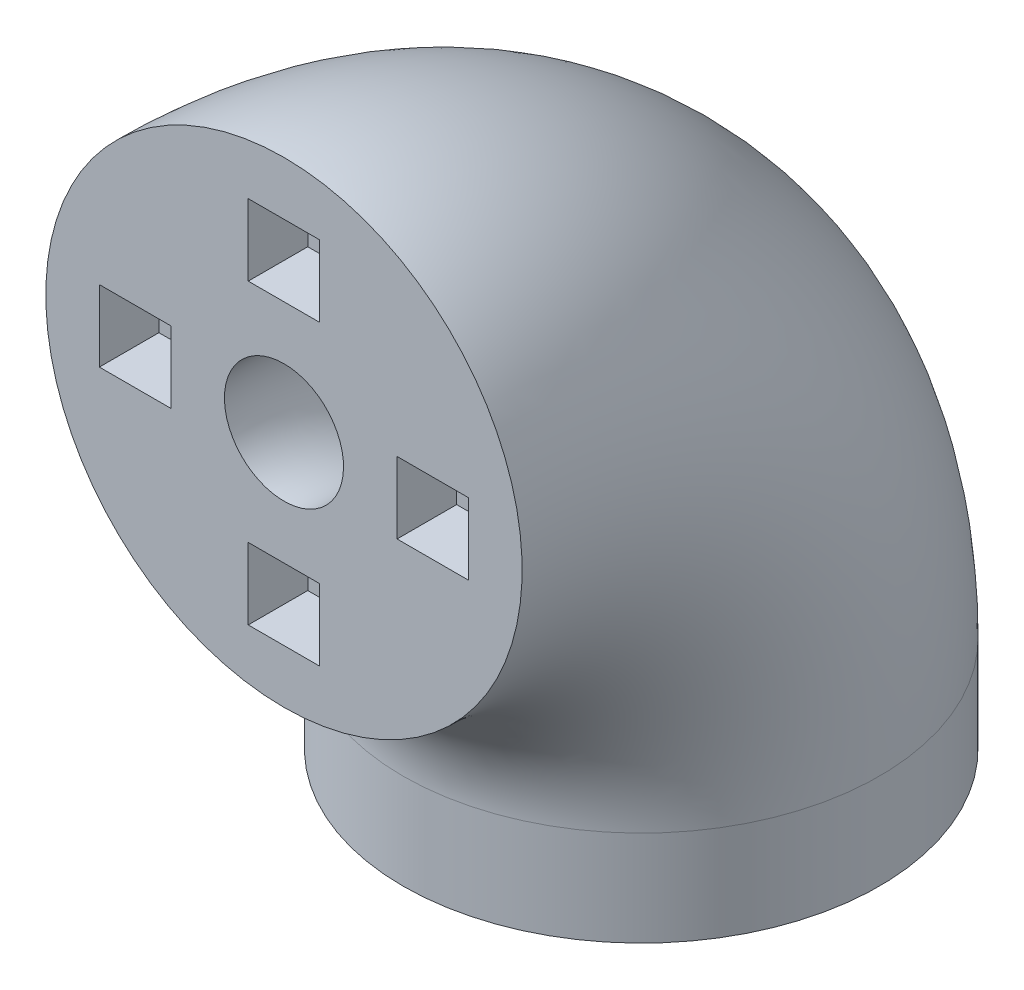
SolidWorks part; units mm, degrees
ref_plane "Front Plane" through (0, 0, 0) normal (0, 0, 1) x (1, 0, 0)
ref_plane "Top Plane" through (0, 0, 0) normal (0, 1, 0) x (1, 0, 0)
ref_plane "Right Plane" through (0, 0, 0) normal (1, 0, 0) x (0, 0, -1)
sketch "Sketch2" plane through (0, 0, 0) normal (1, 0, 0) x (0, 0, -1)
  arc A0 (30, 0) -> (0, 30) centre (0, 0) ccw
  point P6 (30, 0)
  dimension "D3" = 30
sketch "Sketch3" plane through (0, 0, 0) normal (0, 1, 0) x (1, 0, 0)
  circle A0 centre (0, 30) radius 5
  circle A1 centre (0, 30) radius 20
sweep "Sweep1" add profiles "Sketch3" path "Sketch2"
sketch "Sketch6" plane through (0, 0, 0) normal (0, -1, 0) x (1, 0, 0)
  circle A1 centre (0, -30) radius 20
  circle A2 centre (0, -30) radius 20
  circle A6 centre (0, -30) radius 5 construction
  circle A7 centre (0, -30) radius 5
  dimension "D1" = 0
extrude "Boss-Extrude1" add sketch "Sketch6" along normal blind 8
sketch "Sketch10" plane through (0, 0, 0) normal (0, 0, 1) x (1, 0, 0)
  line L0 (-20, 30) -> (20, 30) construction
  line L1 (0, 50) -> (0, 10) construction
  line L2 (-20, 30) -> (-5, 30) construction
  line L3 (3, 45.5) -> (-3, 45.5)
  line L4 (-15.5, 33) -> (-9.5, 33)
  line L5 (-15.5, 33) -> (-15.5, 27)
  line L6 (-15.5, 27) -> (-9.5, 27)
  line L7 (-9.5, 33) -> (-9.5, 27)
  line L8 (-15.5, 33) -> (-9.5, 27) construction
  line L9 (-15.5, 27) -> (-9.5, 33) construction
  line L10 (3, 45.5) -> (3, 39.5)
  line L11 (3, 39.5) -> (-3, 39.5)
  line L12 (-3, 45.5) -> (-3, 39.5)
  line L13 (15.5, 27) -> (15.5, 33)
  line L14 (15.5, 27) -> (9.5, 27)
  line L15 (9.5, 27) -> (9.5, 33)
  line L16 (15.5, 33) -> (9.5, 33)
  line L17 (-3, 14.5) -> (3, 14.5)
  line L18 (-3, 14.5) -> (-3, 20.5)
  line L19 (-3, 20.5) -> (3, 20.5)
  line L20 (3, 14.5) -> (3, 20.5)
  circle A0 centre (0, 30) radius 20 construction
  circle A1 centre (0, 30) radius 5 construction
  point P12 (-12.5, 30)
  point P32 (0, 30)
  dimension "D1" = 6
  dimension "D2" = 6
  dimension "D3" = 4
extrude "Cut-Extrude5" cut sketch "Sketch10" against normal blind 5
